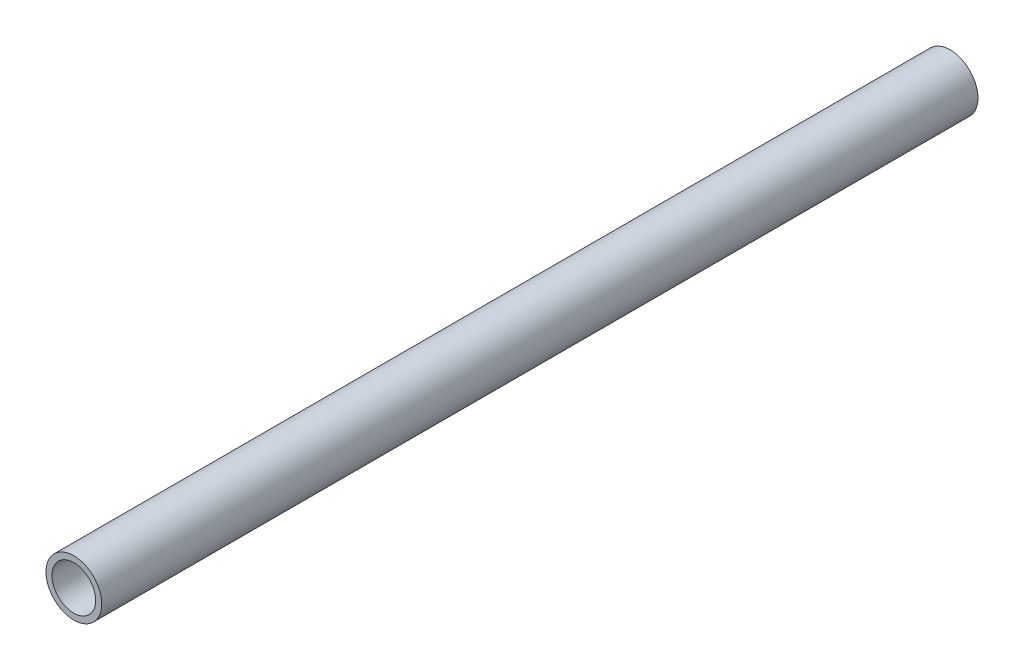
SolidWorks part; units mm, degrees
material "PVC Rigid"
ref_plane "Front Plane" through (0, 0, 0) normal (0, 0, 1) x (1, 0, 0)
ref_plane "Top Plane" through (0, 0, 0) normal (0, 1, 0) x (1, 0, 0)
ref_plane "Right Plane" through (0, 0, 0) normal (1, 0, 0) x (0, 0, -1)
sketch "Sketch1" plane through (0, 0, 0) normal (0, 0, 1) x (1, 0, 0)
  circle A0 centre (0, 0) radius 13.335
  circle A1 centre (0, 0) radius 10.4648
  dimension "D1" = 26.67
  dimension "D2" = 20.9296
extrude "Boss-Extrude1" add sketch "Sketch1" along normal blind 419.1
